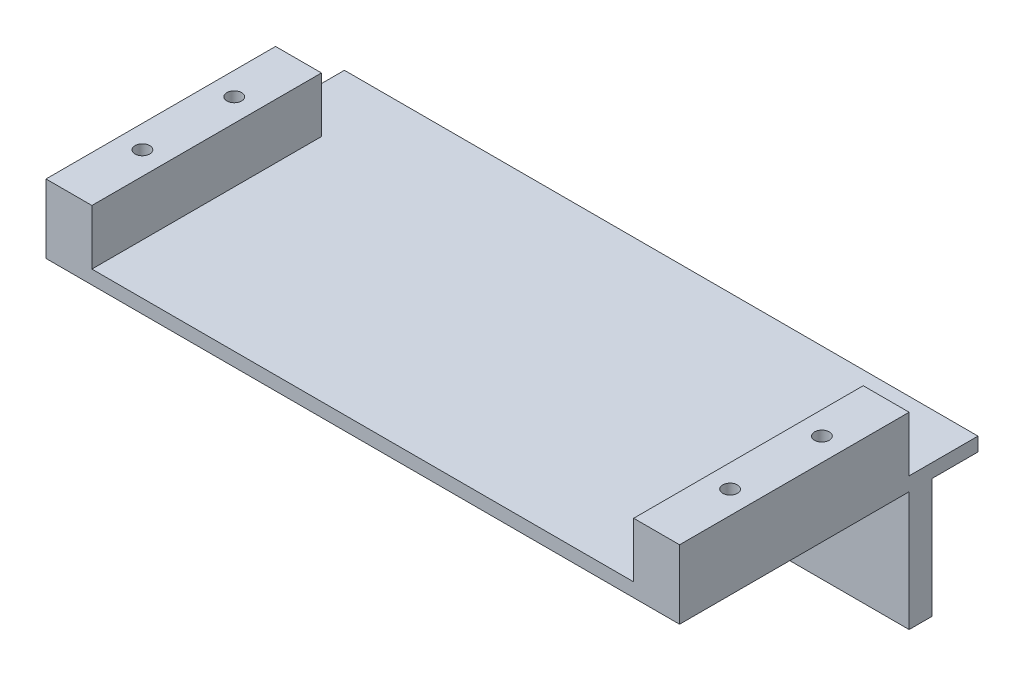
SolidWorks part; units mm, degrees
ref_plane "前视基准面" through (0, 0, 0) normal (0, 0, 1) x (1, 0, 0)
ref_plane "上视基准面" through (0, 0, 0) normal (0, 1, 0) x (1, 0, 0)
ref_plane "右视基准面" through (0, 0, 0) normal (1, 0, 0) x (0, 0, -1)
other "Configuration Table"
sketch "草图1" plane through (0, 0, 0) normal (0, 0, 1) x (1, 0, 0)
  line L0 (-49.798, -1.43) -> (88.202, -1.43) construction
  line L1 (-49.798, 14.57) -> (88.202, 14.57)
  line L2 (-49.798, 14.57) -> (-49.798, -11.43)
  line L3 (-49.798, -11.43) -> (88.202, -11.43)
  line L4 (88.202, 14.57) -> (88.202, -11.43)
  line L5 (19.202, 14.57) -> (19.202, -11.43) construction
  circle A0 centre (-29.798, -1.43) radius 2.1
  circle A1 centre (68.202, -1.43) radius 2.1
  point P12 (0, 0)
  point P13 (0, 0)
  point P14 (85.202, -1.43)
  dimension "D4" = 4.2
  dimension "D1" = 26
  dimension "D2" = 138
  dimension "D3" = 20
  dimension "D5" = 10
extrude "凸台-拉伸1" add sketch "草图1" along normal blind 5
sketch "草图2" plane through (0, 14.57, 0) normal (0, 1, 0) x (1, 0, 0)
  line L0 (88.202, -5) -> (88.202, 0) construction
  line L1 (-49.798, 10) -> (88.202, 10)
  line L2 (-49.798, 10) -> (-49.798, -55)
  line L3 (-49.798, -55) -> (88.202, -55)
  line L4 (88.202, 10) -> (88.202, -55)
  line L6 (-49.798, -5) -> (-49.798, 0) construction
  line L7 (88.202, 0) -> (-49.798, 0) construction
  line L8 (88.202, -5) -> (-49.798, -5) construction
  dimension "D1" = 10
  dimension "D2" = 50
extrude "凸台-拉伸2" add sketch "草图2" along normal blind 3
sketch "草图3" plane through (0, 17.57, 0) normal (0, 1, 0) x (1, 0, 0)
  line L0 (-44.798, -10) -> (-44.798, -55) construction
  line L1 (-49.798, -10) -> (-4.798, -10) construction
  line L2 (-49.798, -10) -> (-49.798, -55) construction
  line L3 (-49.798, -55) -> (-4.798, -55) construction
  line L4 (-4.798, -10) -> (-4.798, -55) construction
  line L5 (-49.798, -39) -> (-44.798, -39) construction
  line L6 (-49.798, -19) -> (-44.798, -19) construction
  line L7 (-49.798, -55) -> (88.202, -55) construction
  line L8 (-49.798, 10) -> (-49.798, -55) construction
  line L9 (83.202, -10) -> (83.202, -55) construction
  line L10 (88.202, -55) -> (78.202, -55) construction
  line L11 (88.202, -55) -> (88.202, -10) construction
  line L12 (88.202, -10) -> (78.202, -10) construction
  line L13 (78.202, -55) -> (78.202, -10) construction
  circle A0 centre (-44.798, -19) radius 1.6
  circle A1 centre (-44.798, -39) radius 1.6
  circle A2 centre (83.202, -19) radius 1.6
  circle A3 centre (83.202, -39) radius 1.6
  point P28 (0, 0)
  point P29 (0, 0)
  dimension "D6" = 3.2
  dimension "D9" = 3.2
  dimension "D1" = 45
  dimension "D2" = 5
  dimension "D3" = 45
  dimension "D4" = 16
  dimension "D5" = 20
  dimension "D7" = 10
  dimension "D8" = 5
extrude "切除-拉伸1" cut sketch "草图3" against normal blind 3
sketch "草图4" plane through (0, 17.57, 0) normal (0, 1, 0) x (1, 0, 0)
  line L0 (19.202, 10) -> (19.202, -55) construction
  line L1 (88.202, -55) -> (78.202, -55)
  line L2 (88.202, -55) -> (88.202, -5)
  line L3 (88.202, -5) -> (78.202, -5)
  line L4 (78.202, -55) -> (78.202, -5)
  line L5 (88.202, 10) -> (-49.798, 10) construction
  line L6 (-49.798, -55) -> (88.202, -55) construction
  line L7 (-49.798, -5) -> (-39.798, -5)
  line L8 (-39.798, -55) -> (-39.798, -5)
  line L9 (-49.798, -55) -> (-39.798, -55)
  line L10 (-49.798, -55) -> (-49.798, -5)
  circle A0 centre (83.202, -19) radius 1.6
  circle A1 centre (83.202, -39) radius 1.6
  circle A2 centre (-44.798, -39) radius 1.6
  circle A3 centre (-44.798, -19) radius 1.6
  dimension "D1" = 10
  dimension "D2" = 50
extrude "凸台-拉伸3" add sketch "草图4" along normal blind 12
